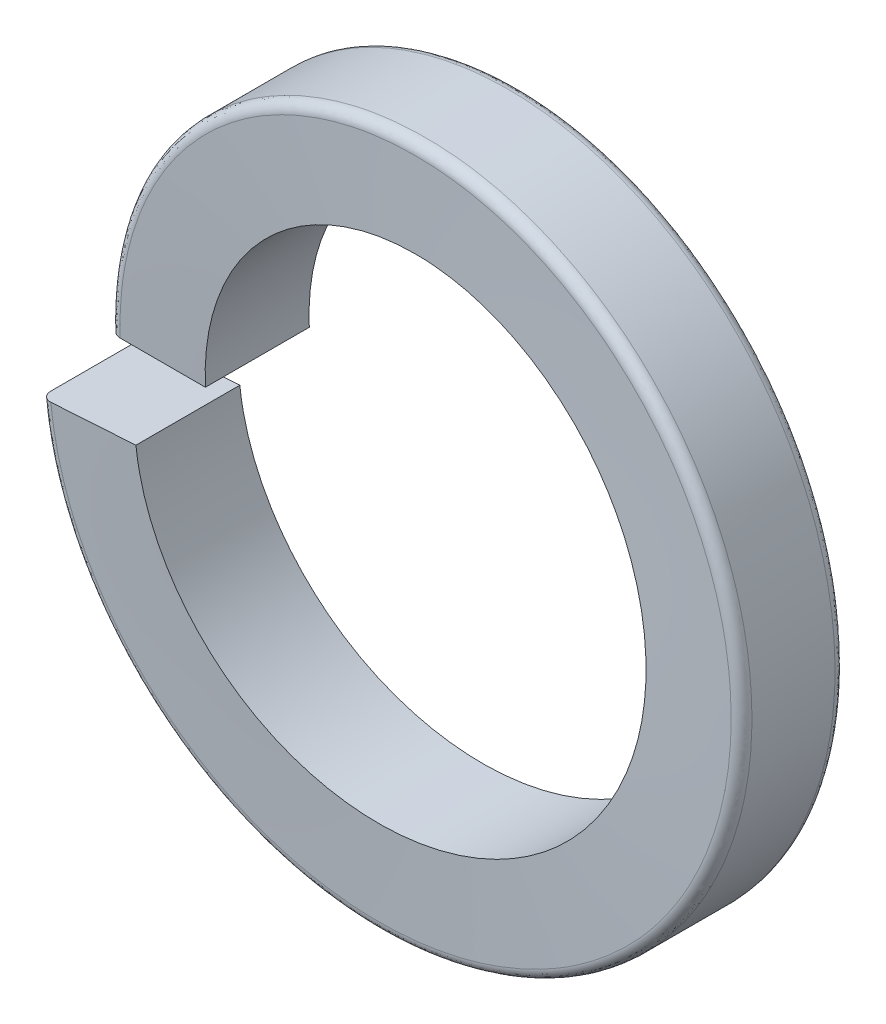
SolidWorks part; units mm, degrees
ref_plane "Front Plane" through (0, 0, 0) normal (0, 0, 1) x (1, 0, 0)
ref_plane "Top Plane" through (0, 0, 0) normal (0, 1, 0) x (1, 0, 0)
ref_plane "Right Plane" through (0, 0, 0) normal (1, 0, 0) x (0, 0, -1)
sketch "Sketch1" plane through (0, 0, 0) normal (0, 0, 1) x (1, 0, 0)
  circle A0 centre (0, 0) radius 3.4925
  dimension "D1" = 6.985
curve "Helix/Spiral1" pitch 0.8636 height 0.855 turns 0.99
sketch "Sketch2" plane through (0, 0, 0) normal (0, 1, 0) x (1, 0, 0)
  line L1 (2.908, 0.2032) -> (4.0764, 0.2032)
  line L2 (2.908, 0.2032) -> (2.908, -1.0668)
  line L3 (2.908, -1.0668) -> (4.0764, -1.0668)
  line L4 (4.0764, 0.2032) -> (4.0764, -1.0668)
  line L5 (2.908, 0.2032) -> (4.0764, -1.0668) construction
  line L6 (2.908, -1.0668) -> (4.0764, 0.2032) construction
  point P0 (3.4922, -0.4318)
  dimension "D1" = 1.27
  dimension "D2" = 1.1684
sweep "Sweep3" add profiles "Sketch2" path "Helix/Spiral1"
fillet "Fillet1" radius 0.127 2 edges
